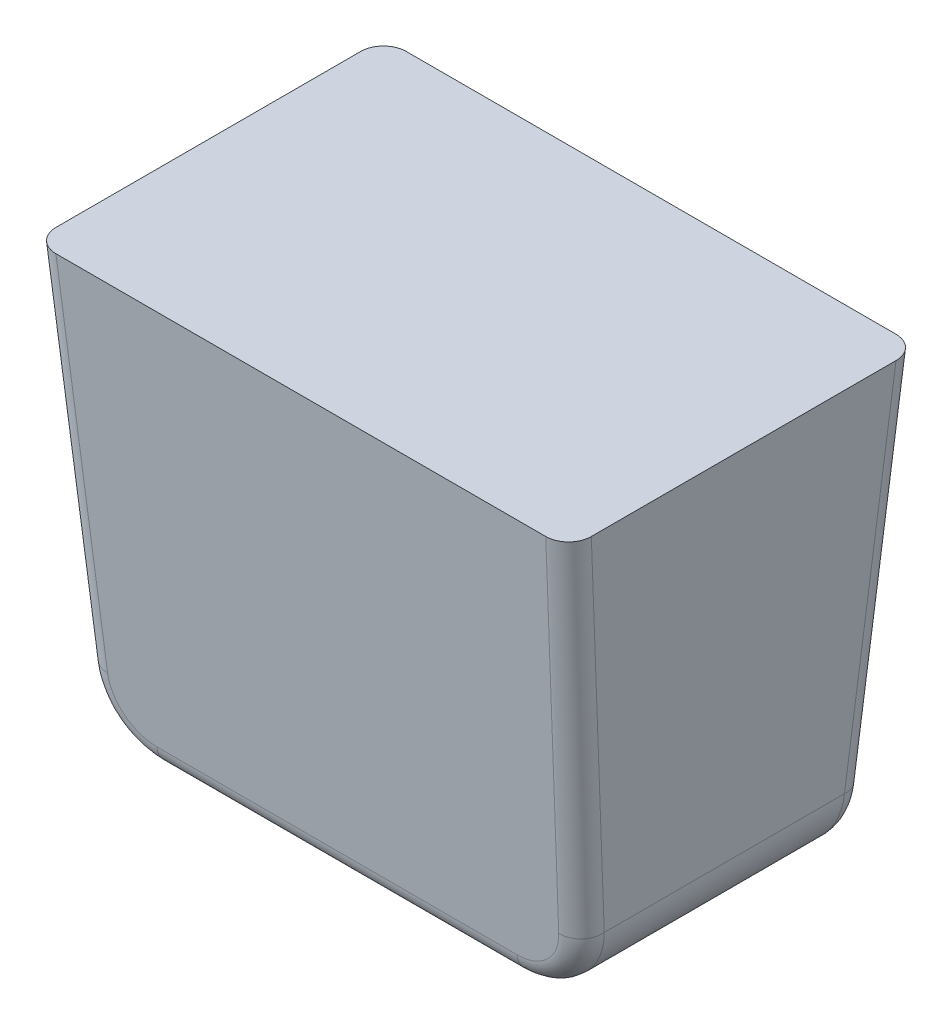
SolidWorks part; units mm, degrees
ref_plane "Front Plane" through (0, 0, 0) normal (0, 0, 1) x (1, 0, 0)
ref_plane "Top Plane" through (0, 0, 0) normal (0, 1, 0) x (1, 0, 0)
ref_plane "Right Plane" through (0, 0, 0) normal (1, 0, 0) x (0, 0, -1)
sketch "Sketch2" plane through (0, 0, 0) normal (0, 1, 0) x (1, 0, 0)
  line L1 (23.75, 15.8333) -> (-23.75, 15.8333)
  line L2 (23.75, 15.8333) -> (23.75, -15.8333)
  line L3 (23.75, -15.8333) -> (-23.75, -15.8333)
  line L4 (-23.75, 15.8333) -> (-23.75, -15.8333)
  line L5 (23.75, 15.8333) -> (-23.75, -15.8333) construction
  line L6 (23.75, -15.8333) -> (-23.75, 15.8333) construction
  point P0 (0, 0)
  dimension "D1" = 31.6667
  dimension "D2" = 47.5
extrude "Boss-Extrude1" add sketch "Sketch2" along normal blind 43.5
draft "Draft2" type of draft neutral plane draft angle 5 faces to draft 1 face at (0, 21.75, 15.8333) neutral plane through (0, 43.5, 0) neutral plane normal (0, 1, 0) reverse direction yes parameters "D1"=5
draft "Draft3" type of draft neutral plane draft angle 5 faces to draft 1 face at (0, 21.75, -15.8333) neutral plane through (0, 43.5, 0) neutral plane normal (0, 1, 0) reverse direction yes parameters "D1"=5
draft "Draft4" type of draft neutral plane draft angle 3 faces to draft 1 face at (-23.75, 21.75, 0) neutral plane through (0, 43.5, 0) neutral plane normal (0, 1, 0) reverse direction yes parameters "D1"=3
draft "Draft5" type of draft neutral plane draft angle 3 faces to draft 1 face at (23.75, 21.75, 0) neutral plane through (0, 43.5, 0) neutral plane normal (0, 1, 0) reverse direction yes parameters "D1"=3
fillet "Fillet1" radius 6 2 edges at (-21.4703, 0, 0) (21.4703, 0, 0)
fillet "Fillet2" radius 2 14 edges at (22.7591, 24.593, 14.1792) (19.9066, 1.6478, 12.1717) (0, 0, 12.0276) (-19.9066, 1.6478, 12.1717) (22.7591, 24.593, -14.1792) (19.9066, 1.6478, -12.1717) (0, 0, -12.0276) (-19.9066, 1.6478, -12.1717) (0, 43.5, -15.8333) (23.75, 43.5, 0) (0, 43.5, 15.8333) (-23.75, 43.5, 0) (-22.7591, 24.593, 14.1792) (-22.7591, 24.593, -14.1792)
sketch "Sketch3" plane through (0, 43.5, 0) normal (0, 1, 0) x (1, 0, 0)
  line L1 (32.9636, -20.7033) -> (-32.9636, -20.7033)
  line L2 (32.9636, -20.7033) -> (32.9636, 20.7033)
  line L3 (32.9636, 20.7033) -> (-32.9636, 20.7033)
  line L4 (-32.9636, -20.7033) -> (-32.9636, 20.7033)
  line L5 (32.9636, -20.7033) -> (-32.9636, 20.7033) construction
  line L6 (32.9636, 20.7033) -> (-32.9636, -20.7033) construction
  point P0 (0, 0)
extrude "Cut-Extrude1" cut sketch "Sketch3" against normal blind 5.5
